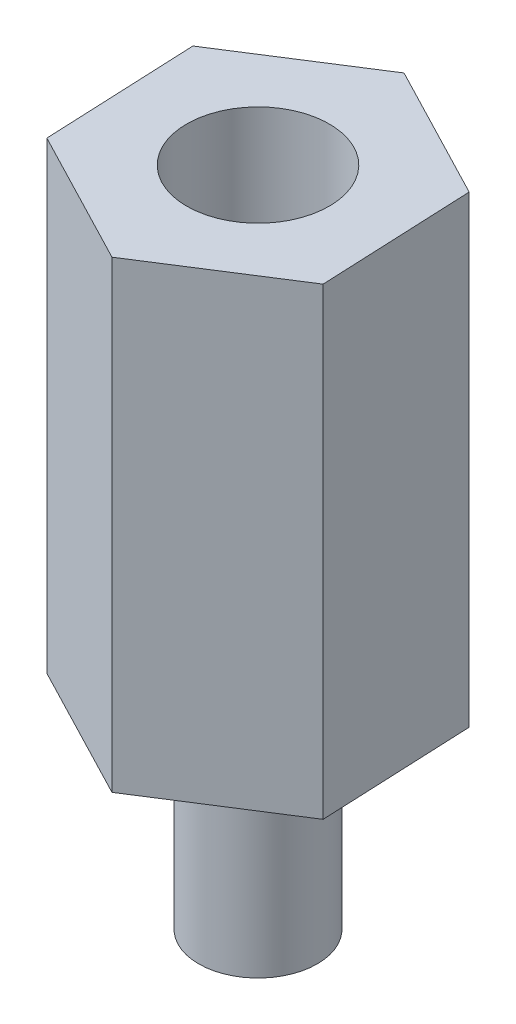
SolidWorks part; units mm, degrees
ref_plane "Front Plane" through (0, 0, 0) normal (0, 0, 1) x (1, 0, 0)
ref_plane "Top Plane" through (0, 0, 0) normal (0, 1, 0) x (1, 0, 0)
ref_plane "Right Plane" through (0, 0, 0) normal (1, 0, 0) x (0, 0, -1)
sketch "Sketch1" plane through (0, 0, 0) normal (0, 1, 0) x (1, 0, 0)
  line L1 (3.2527, -1.6914) -> (3.0911, 1.9712)
  line L2 (3.0911, 1.9712) -> (-0.1616, 3.6626)
  line L3 (-0.1616, 3.6626) -> (-3.2527, 1.6914)
  line L4 (-3.2527, 1.6914) -> (-3.0911, -1.9712)
  line L5 (-3.0911, -1.9712) -> (0.1616, -3.6626)
  line L6 (0.1616, -3.6626) -> (3.2527, -1.6914)
  circle A0 centre (0, 0) radius 3.175 construction
  dimension "D1" = 6.35
extrude "Boss-Extrude1" add sketch "Sketch1" along normal blind 11.1125
sketch "Sketch2" plane through (0, 0, 0) normal (0, -1, 0) x (1, 0, 0)
  circle A0 centre (0, 0) radius 1.4224
  dimension "D1" = 2.8448
extrude "Boss-Extrude2" add sketch "Sketch2" along normal blind 4.7625
sketch "Sketch3" plane through (0, 11.1125, 0) normal (0, 1, 0) x (1, 0, 0)
  circle A0 centre (0, 0) radius 1.7089
extrude "Cut-Extrude1" cut sketch "Sketch3" against normal blind 6.35
